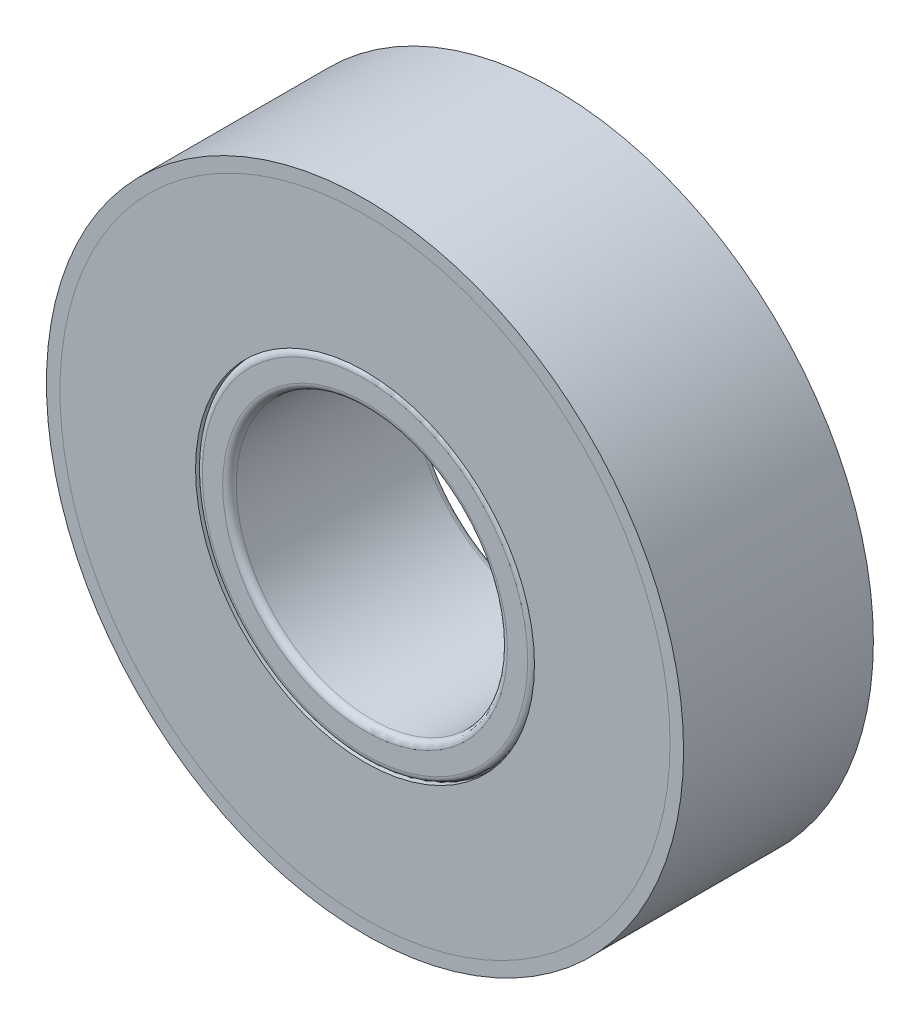
SolidWorks part; units mm, degrees
ref_plane "Front Plane" through (0, 0, 0) normal (0, 0, 1) x (1, 0, 0)
ref_plane "Top Plane" through (0, 0, 0) normal (0, 1, 0) x (1, 0, 0)
ref_plane "Right Plane" through (0, 0, 0) normal (1, 0, 0) x (0, 0, -1)
sketch "Sketch1" plane through (0, 0, 0) normal (0, 0, 1) x (1, 0, 0)
  circle A0 centre (0, 0) radius 23.5
  circle A1 centre (0, 0) radius 10
  dimension "D1" = 20
  dimension "D2" = 47
extrude "Boss-Extrude1" add sketch "Sketch1" along normal blind 14
sketch "Sketch2" plane through (0, 0, 14) normal (0, 0, 1) x (1, 0, 0)
  circle A0 centre (0, 0) radius 12.5
  circle A1 centre (0, 0) radius 22.5
  dimension "D1" = 25
  dimension "D2" = 45
extrude "Cut-Extrude1" cut sketch "Sketch2" against normal blind 14
sketch "Sketch3" plane through (0, 0, 0) normal (1, 0, 0) x (0, 0, -1)
  line L7 (-6.8226, 22.5) -> (-6.8226, 12.4937)
  arc A2 (-6.8226, 12.4937) -> (-6.8226, 22.5) centre (-6.8226, 17.4969) ccw
revolve "Revolve1" add sketch "Sketch3" angle 360 about L7
pattern_circular "Circular-Pattern1" count 10 over 360 about axis through (0, 0, 0) along (0, 0, 1) of "Revolve1"
fillet "Fillet1" radius 0.5 1 edges at (10, 0, 0)
fillet "Fillet3" radius 0.5 1 edges at (12.5, 0, 0)
sketch "Sketch5" plane through (0, 0, 0) normal (0, 0, 1) x (1, 0, 0)
  circle A0 centre (0, 0) radius 12.5
  circle A1 centre (0, 0) radius 22.5
  dimension "D1" = 25
  dimension "D2" = 45
extrude "Boss-Extrude3" add sketch "Sketch5" along normal blind 0.5 separate body
sketch "Sketch6" plane through (0, 0, 14) normal (0, 0, 1) x (1, 0, 0)
  circle A0 centre (0, 0) radius 12.5
  circle A1 centre (0, 0) radius 22.5
  dimension "D1" = 25
  dimension "D2" = 45
extrude "Boss-Extrude4" add sketch "Sketch6" against normal blind 0.5 separate body
fillet "Fillet5" radius 0.5 1 edges at (12.5, 0, 14)
fillet "Fillet6" radius 0.5 1 edges at (10, 0, 14)
